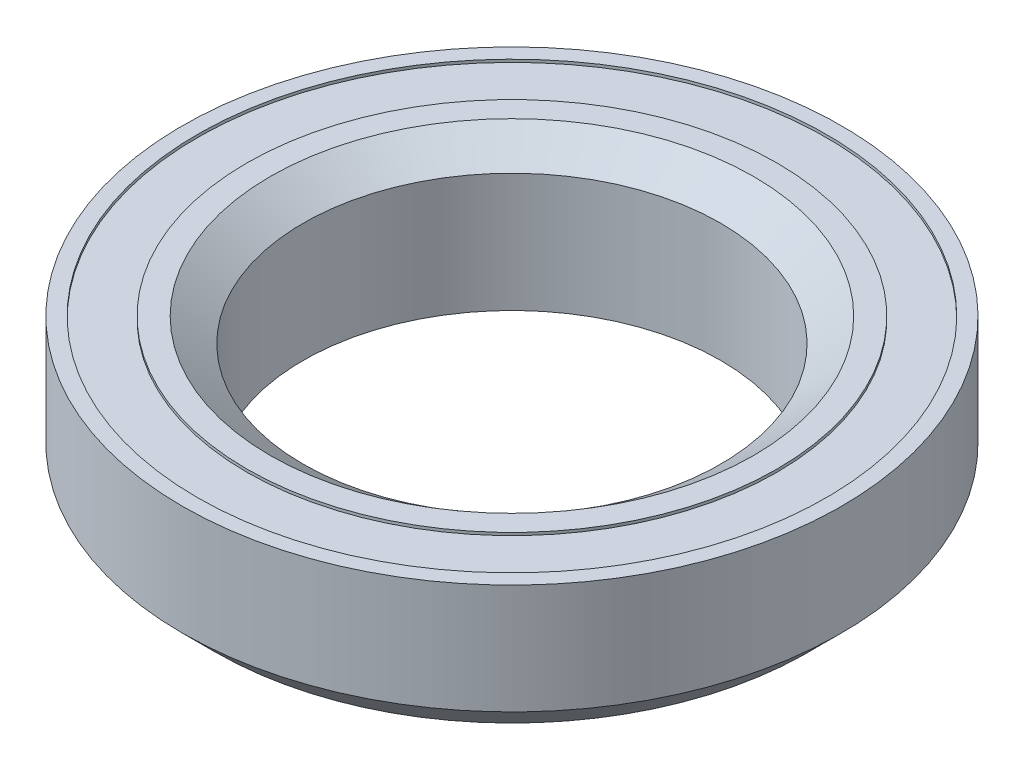
SolidWorks part; units mm, degrees
material "1.4000 (X6Cr13)"
ref_plane "Front Plane" through (0, 0, 0) normal (0, 0, 1) x (1, 0, 0)
ref_plane "Top Plane" through (0, 0, 0) normal (0, 1, 0) x (1, 0, 0)
ref_plane "Right Plane" through (0, 0, 0) normal (1, 0, 0) x (0, 0, -1)
sketch "Sketch1" plane through (0, 0, 0) normal (0, 1, 0) x (1, 0, 0)
  circle A0 centre (0, 0) radius 15
  dimension "D1" = 30
extrude "Boss-Extrude1" add sketch "Sketch1" along normal blind 6.5
sketch "Sketch2" plane through (0, 6.5, 0) normal (0, 1, 0) x (1, 0, 0)
  circle A0 centre (0, 0) radius 9.5
  dimension "D1" = 19
extrude "Cut-Extrude1" cut sketch "Sketch2" against normal through all
chamfer "Chamfer1" distance 1.5 angle 45 1 edges at (0, 0, 15)
chamfer "Chamfer2" distance 1.5 angle 36 1 edges at (0, 6.5, 9.5)
sketch "Sketch3" plane through (0, 0, 0) normal (0, -1, 0) x (1, 0, 0)
  circle A0 centre (0, 0) radius 12.8905
  circle A1 centre (0, 0) radius 10.2232
  dimension "D1" = 25.781
extrude "Cut-Extrude2" cut sketch "Sketch3" against normal blind 0.127
sketch "Sketch4" plane through (0, 6.5, 0) normal (0, 1, 0) x (1, 0, 0)
  circle A1 centre (0, 0) radius 12.065
  circle A2 centre (0, 0) radius 14.316
  dimension "D1" = 24.13
extrude "Cut-Extrude3" cut sketch "Sketch4" against normal blind 0.127
